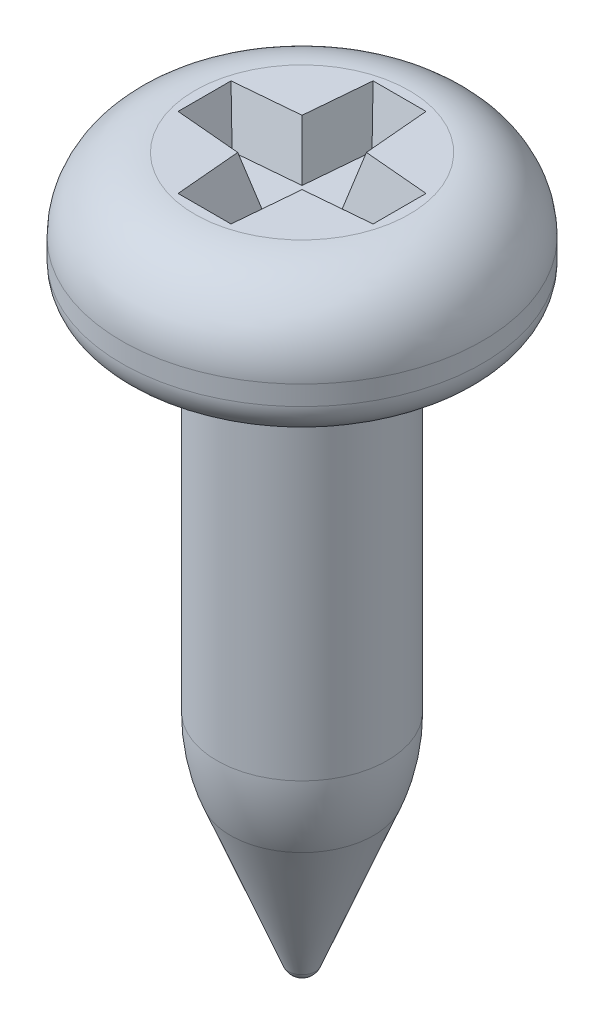
SolidWorks part; units mm, degrees
ref_plane "Front Plane" through (0, 0, 0) normal (0, 0, 1) x (1, 0, 0)
ref_plane "Top Plane" through (0, 0, 0) normal (0, 1, 0) x (1, 0, 0)
ref_plane "Right Plane" through (0, 0, 0) normal (1, 0, 0) x (0, 0, -1)
sketch "Sketch1" plane through (0, 0, 0) normal (0, 0, 1) x (1, 0, 0)
  line L0 (0, 0) -> (0, -7.3) construction
  line L2 (0.875, -4.9644) -> (0.875, -1.45)
  line L3 (1.025, -1.3) -> (1.5, -1.3)
  line L4 (1.85, -0.95) -> (1.85, -0.75)
  line L5 (1.1, 0) -> (0, 0)
  line L6 (0, 0) -> (0, -7.3)
  line L7 (0.7348, -5.7) -> (0.1395, -7.2052)
  arc A0 (1.85, -0.75) -> (1.1, 0) centre (1.1, -0.75) ccw
  arc A1 (1.5, -1.3) -> (1.85, -0.95) centre (1.5, -0.95) ccw
  arc A2 (0.875, -1.45) -> (1.025, -1.3) centre (1.025, -1.45) cw
  arc A3 (0.1395, -7.2052) -> (0, -7.3) centre (0, -7.15) cw
  arc A4 (0.7348, -5.7) -> (0.875, -4.9644) centre (-1.125, -4.9644) ccw
  point P13 (0.875, -1.3)
  dimension "D3" = 0.75
  dimension "D6" = 0.35
  dimension "D7" = 0.15
  dimension "D8" = 2
  dimension "D4" = 1.6
  dimension "D10" = 0.15
  dimension "D1" = 3.7
  dimension "D2" = 1.3
  dimension "D5" = 1.75
  dimension "D9" = 6
revolve "Revolve1" add sketch "Sketch1" angle 360 about L0
sketch "Sketch2" plane through (0, 0, 0) normal (0, 1, 0) x (1, 0, 0)
  line L0 (0, 1) -> (0, 0) construction
  line L1 (0, 0) -> (1, 0) construction
  line L2 (-0.2714, 1) -> (0.2714, 1)
  line L3 (0.2714, 1) -> (0.33, 0.33)
  line L4 (0.33, 0.33) -> (1, 0.2714)
  line L5 (1, 0.2714) -> (1, -0.2714)
  line L6 (-1, 0.2714) -> (-1, -0.2714)
  line L7 (-0.33, 0.33) -> (-1, 0.2714)
  line L8 (-0.2714, 1) -> (-0.33, 0.33)
  line L9 (-0.33, -0.33) -> (-1, -0.2714)
  line L10 (-0.2714, -1) -> (-0.33, -0.33)
  line L11 (-0.2714, -1) -> (0.2714, -1)
  line L12 (0.2714, -1) -> (0.33, -0.33)
  line L13 (0.33, -0.33) -> (1, -0.2714)
  point P18 (-1, 0)
  point P26 (0, 0)
  dimension "D1" = 95
  dimension "D2" = 2
  dimension "D3" = 0.66
extrude "Cut-Extrude1" cut sketch "Sketch2" against normal blind 0.5 draft 15
